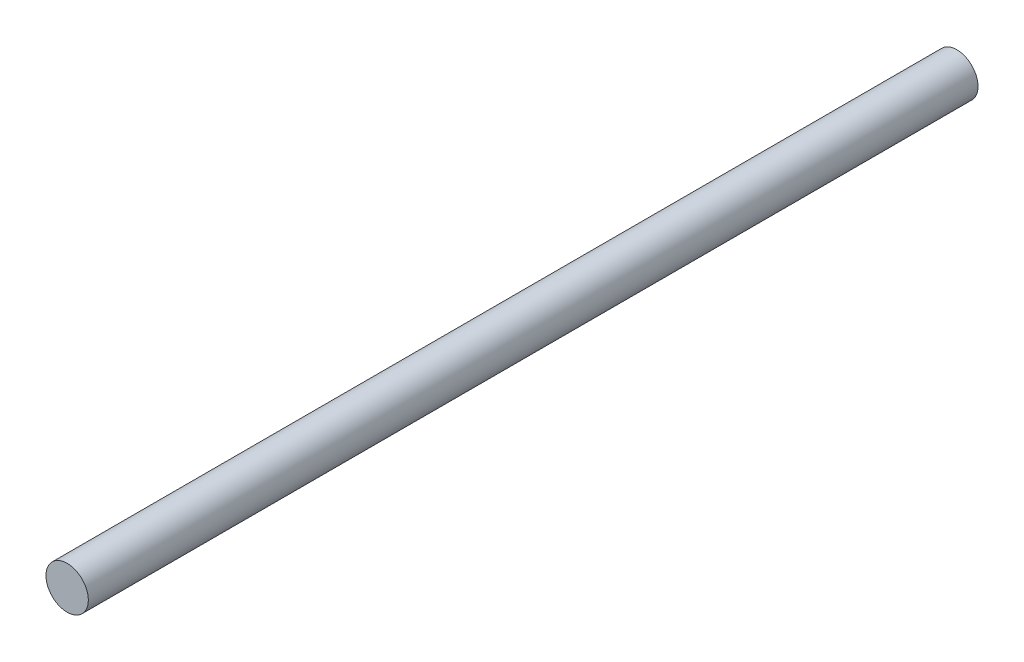
SolidWorks part; units mm, degrees
ref_plane "正面" through (0, 0, 0) normal (0, 0, 1) x (1, 0, 0)
ref_plane "平面" through (0, 0, 0) normal (0, 1, 0) x (1, 0, 0)
ref_plane "右側面" through (0, 0, 0) normal (1, 0, 0) x (0, 0, -1)
sketch "ｽｹｯﾁ1" plane through (0, 0, 0) normal (0, 0, 1) x (1, 0, 0)
  circle A0 centre (0, 0) radius 1.5
  dimension "D1" = 3
extrude "ﾎﾞｽ - 押し出し1" add sketch "ｽｹｯﾁ1" along normal blind 63
